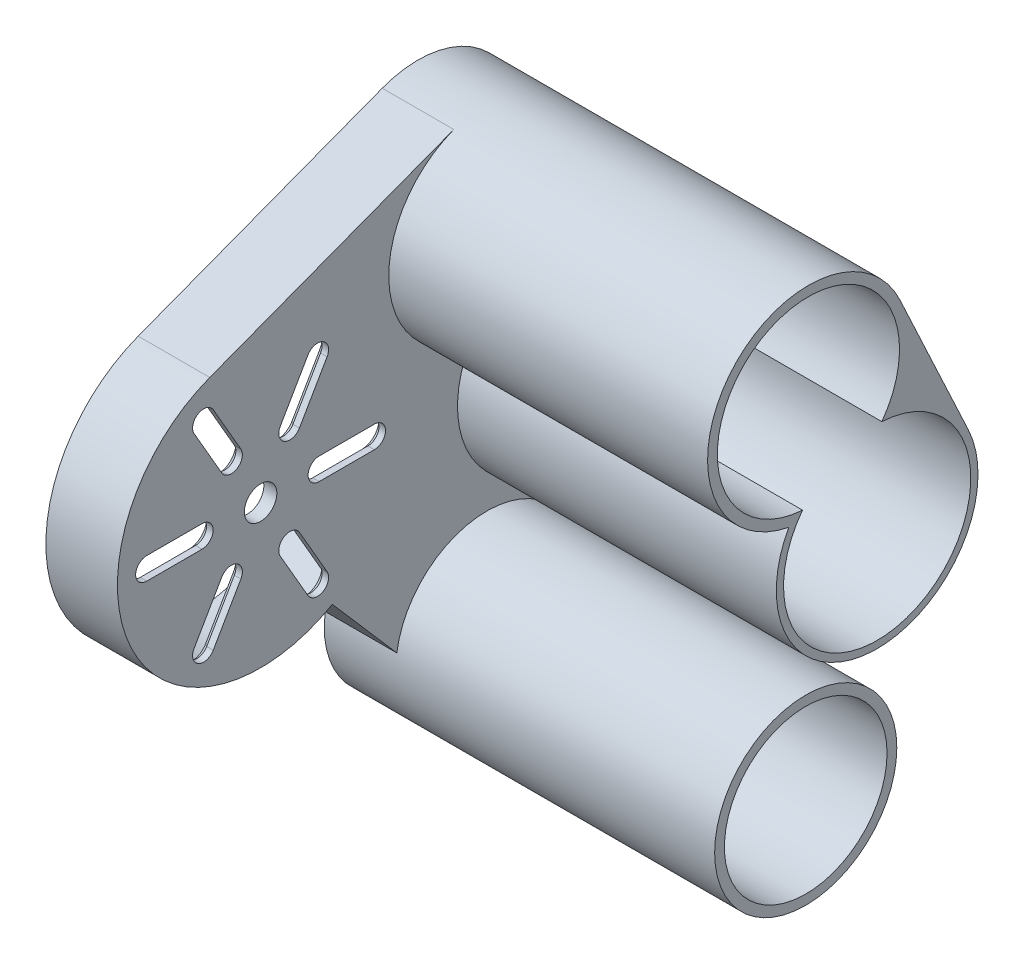
SolidWorks part; units mm, degrees
material "ABS"
ref_plane "Front Plane" through (0, 0, 0) normal (0, 0, 1) x (1, 0, 0)
ref_plane "Top Plane" through (0, 0, 0) normal (0, 1, 0) x (1, 0, 0)
ref_plane "Right Plane" through (0, 0, 0) normal (1, 0, 0) x (0, 0, -1)
sketch "Sketch1" plane through (0, 0, 0) normal (1, 0, 0) x (0, 0, -1)
  line L0 (-34.7866, 32.5023) -> (0.4149, 52.8259) construction
  line L1 (0.4149, 52.8259) -> (10.9803, 30.1682) construction
  line L2 (10.9803, 30.1682) -> (0, 0) construction
  line L3 (-34.7866, 32.5023) -> (-57.7866, 32.5023) construction
  line L4 (-43.7866, 32.5023) -> (-52.2866, 32.5023) construction
  line L5 (-43.7866, 30.8023) -> (-52.2866, 30.8023)
  line L6 (-43.7866, 34.2023) -> (-52.2866, 34.2023)
  line L9 (-23.7656, 13.4619) -> (-13.8521, 2.0298)
  line L12 (7.7696, 45.332) -> (1.428, 42.3749) construction
  line L13 (10.6233, 41.1624) -> (2.7877, 37.5086) construction
  line L14 (14.4626, 59.3765) -> (25.0281, 36.7188)
  line L15 (13.1053, -4.9244) -> (22.3217, 19.603)
  line L16 (-39.2866, 40.2965) -> (-43.5366, 47.6578) construction
  line L17 (-40.7588, 39.4465) -> (-45.0088, 46.8078)
  line L18 (-37.8144, 41.1465) -> (-42.0644, 48.5078)
  line L19 (-30.2866, 40.2965) -> (-26.0366, 47.6578) construction
  line L20 (-31.7588, 41.1465) -> (-27.5088, 48.5078)
  line L21 (-28.8144, 39.4465) -> (-24.5644, 46.8078)
  line L22 (-25.7866, 32.5023) -> (-17.2866, 32.5023) construction
  line L23 (-25.7866, 34.2023) -> (-17.2866, 34.2023)
  line L24 (-25.7866, 30.8023) -> (-17.2866, 30.8023)
  line L25 (-30.2866, 24.7081) -> (-26.0366, 17.3469) construction
  line L26 (-28.8144, 25.5581) -> (-24.5644, 18.1969)
  line L27 (-31.7588, 23.8581) -> (-27.5088, 16.4969)
  line L28 (-39.2866, 24.7081) -> (-43.5366, 17.3469) construction
  line L29 (-37.8144, 23.8581) -> (-42.0644, 16.4969)
  line L30 (-40.7588, 25.5581) -> (-45.0088, 18.1969)
  line L31 (-39.2866, 40.2965) -> (-34.7866, 32.5023) construction
  line L32 (-34.7866, 32.5023) -> (-30.2866, 40.2965) construction
  line L33 (-25.7866, 32.5023) -> (-34.7866, 32.5023) construction
  line L34 (-30.2866, 24.7081) -> (-34.7866, 32.5023) construction
  line L35 (-39.2866, 24.7081) -> (-34.7866, 32.5023) construction
  line L36 (-42.5983, 53.0687) -> (-5.0888, 67.3159)
  line L37 (0.3482, 32.9891) -> (-7.8517, 2.0832) construction
  line L38 (7.3539, -3.4512) -> (20.9383, 25.4949) construction
  line L41 (0, 0) -> (-13.8521, 2.0298) construction
  line L43 (0, 0) -> (41.0697, 0) construction
  arc A4 (-43.7866, 30.8023) -> (-43.7866, 34.2023) centre (-43.7866, 32.5023) ccw
  arc A5 (-52.2866, 34.2023) -> (-52.2866, 30.8023) centre (-52.2866, 32.5023) ccw
  circle A6 centre (-34.7866, 32.5023) radius 2.5
  circle A7 centre (0, 0) radius 2.5
  arc A8 (-13.8521, 2.0298) -> (13.1053, -4.9244) centre (0, 0) ccw
  circle A9 centre (-34.7866, 32.5023) radius 22 construction
  circle A11 centre (10.9803, 30.1682) radius 2.5
  circle A12 centre (-34.7866, 32.5023) radius 23 construction
  circle A14 centre (0.4149, 52.8259) radius 2.5
  circle A15 centre (0.4149, 52.8259) radius 15.5 construction
  circle A16 centre (0.4149, 52.8259) radius 10.5 construction
  circle A17 centre (10.9803, 30.1682) radius 11 construction
  circle A18 centre (10.9803, 30.1682) radius 15.5 construction
  arc A19 (-40.7588, 39.4465) -> (-37.8144, 41.1465) centre (-39.2866, 40.2965) ccw
  arc A20 (-42.0644, 48.5078) -> (-45.0088, 46.8078) centre (-43.5366, 47.6578) ccw
  arc A21 (-31.7588, 41.1465) -> (-28.8144, 39.4465) centre (-30.2866, 40.2965) ccw
  arc A22 (-24.5644, 46.8078) -> (-27.5088, 48.5078) centre (-26.0366, 47.6578) ccw
  arc A23 (-25.7866, 34.2023) -> (-25.7866, 30.8023) centre (-25.7866, 32.5023) ccw
  arc A24 (-17.2866, 30.8023) -> (-17.2866, 34.2023) centre (-17.2866, 32.5023) ccw
  arc A25 (-28.8144, 25.5581) -> (-31.7588, 23.8581) centre (-30.2866, 24.7081) ccw
  arc A26 (-27.5088, 16.4969) -> (-24.5644, 18.1969) centre (-26.0366, 17.3469) ccw
  arc A27 (-37.8144, 23.8581) -> (-40.7588, 25.5581) centre (-39.2866, 24.7081) ccw
  arc A28 (-45.0088, 18.1969) -> (-42.0644, 16.4969) centre (-43.5366, 17.3469) ccw
  circle A29 centre (0, 0) radius 8.1234 construction
  arc A30 (-5.0888, 67.3159) -> (14.4626, 59.3765) centre (0.4149, 52.8259) cw
  circle A31 centre (0, 0) radius 14 construction
  arc A32 (25.0281, 36.7188) -> (22.3217, 19.603) centre (10.9803, 30.1682) cw
  circle A33 centre (-34.7866, 32.5023) radius 9 construction
  circle A34 centre (-34.7866, 32.5023) radius 17.5 construction
  arc A35 (-42.5983, 53.0687) -> (-23.7656, 13.4619) centre (-34.7866, 32.5023) ccw
  point P12 (-48.0366, 32.5023)
  point P44 (-41.4116, 43.9771)
  point P51 (-28.1616, 43.9771)
  point P58 (-21.5366, 32.5023)
  point P65 (-28.1616, 21.0275)
  point P72 (-41.4116, 21.0275)
  dimension "D2" = 5
  dimension "D3" = 5
  dimension "D4" = 32.1043
  dimension "D5" = 25
  dimension "D7" = 44
  dimension "D9" = 21
  dimension "D11" = 31
  dimension "D12" = 16.2468
  dimension "D16" = 70
  dimension "D17" = 18
  dimension "D8" = 31
  dimension "D10" = 22
  dimension "D13" = 28
  dimension "D14" = 35
  dimension "D20" = 46
  dimension "D6" = 135
  dimension "D15" = 85
  dimension "D19" = 3.4
  dimension "D18" = 6
extrude "Boss-Extrude1" add sketch "Sketch1" along normal blind 50 and the other way blind 10
sketch "Sketch2" plane through (-10, 0, 0) normal (-1, 0, 0) x (0, 0, 1)
  line L0 (38.6871, 54.5543) -> (38.1899, 53.2456) construction
  line L1 (42.5983, 53.0687) -> (5.0888, 67.3159) construction
  line L2 (-13.1053, -4.9244) -> (-22.3217, 19.603) construction
  line L3 (27.472, 13.2447) -> (10.0077, 19.8781)
  line L4 (10.0077, 19.8781) -> (12.4846, 1.7013)
  line L6 (42.1012, 51.76) -> (4.5917, 66.0071)
  line L11 (-11.7948, -4.432) -> (-21.4204, 21.1844)
  line L12 (-23.5382, 35.8254) -> (-13.2706, 58.6173)
  arc A0 (27.472, 13.2447) -> (42.1012, 51.76) centre (34.7866, 32.5023) ccw
  arc A2 (-11.7948, -4.432) -> (12.4846, 1.7013) centre (0, 0) ccw
  arc A3 (-21.4204, 21.1844) -> (-23.5382, 35.8254) centre (-10.9803, 30.1682) cw
  arc A4 (-13.2706, 58.6173) -> (4.5917, 66.0071) centre (-0.4149, 52.8259) cw
  dimension "D1" = 1.4
  dimension "D2" = 1.4
extrude "Cut-Extrude1" cut sketch "Sketch2" against normal blind 9
sketch "Sketch3" plane through (50, 0, 0) normal (1, 0, 0) x (0, 0, -1)
  line L1 (-42.5983, 53.0687) -> (-5.0888, 67.3159) construction
  line L2 (22.3217, 19.603) -> (13.1053, -4.9244)
  line L3 (-5.0888, 67.3159) -> (-55.4269, 48.1961)
  line L4 (-55.4269, 48.1961) -> (-58.2869, 17.3245)
  line L5 (-58.2869, 17.3245) -> (-13.8521, 2.0298)
  line L6 (14.4626, 59.3765) -> (25.0281, 36.7188)
  arc A0 (-2.6089, 37.6237) -> (-5.0888, 67.3159) centre (0.4149, 52.8259) cw
  circle A1 centre (0.4149, 52.8259) radius 15.5 construction
  arc A2 (-2.6089, 37.6237) -> (22.3217, 19.603) centre (10.9803, 30.1682) ccw
  circle A3 centre (10.9803, 30.1682) radius 15.5 construction
  arc A4 (13.1053, -4.9244) -> (-13.8521, 2.0298) centre (0, 0) ccw
  circle A6 centre (0.4149, 52.8259) radius 14
  circle A7 centre (10.9803, 30.1682) radius 14.3914
  circle A8 centre (0, 0) radius 12.5
  arc A9 (14.4626, 59.3765) -> (14.004, 45.3704) centre (0.4149, 52.8259) cw
  arc A10 (25.0281, 36.7188) -> (14.004, 45.3704) centre (10.9803, 30.1682) ccw
  arc A11 (-42.5983, 53.0687) -> (-23.7656, 13.4619) centre (-34.7866, 32.5023) ccw construction
extrude "Cut-Extrude2" cut sketch "Sketch3" against normal blind 49
chamfer "Chamfer1" distance 1 angle 45 24 edges at (-1, 21.8775, 26.6894) (-1, 26.1803, 31.1366) (-1, 15.8746, 25.1866) (-1, 20.1775, 29.6338) (-1, 20.1775, 39.9394) (-1, 26.1803, 38.4366) (-1, 15.8746, 44.3866) (-1, 21.8775, 42.8838) (-1, 30.8023, 48.0366) (-1, 32.5023, 42.0866) (-1, 32.5023, 53.9866) (-1, 34.2023, 48.0366) (-1, 43.1271, 42.8838) (-1, 38.8243, 38.4366) (-1, 49.13, 44.3866) (-1, 44.8271, 39.9394) (-1, 49.13, 25.1866) (-1, 44.8271, 29.6338) (-1, 38.8243, 31.1366) (-1, 43.1271, 26.6894) (-1, 32.5023, 27.4866) (-1, 30.8023, 21.5366) (-1, 32.5023, 15.5866) (-1, 34.2023, 21.5366)
chamfer "Chamfer3" distance 0.25 angle 45 10 edges at (-1, 65.8549, -5.8051) (-1, 47.2213, -18.4044) (-1, 28.1964, -24.6117) (-1, 8.3762, -16.6076) (-1, -12.2163, 3.086) (-1, 10.7897, 11.2461) (-1, 16.5614, 18.7398) (-1, 25.1877, 54.0442) (-1, 58.8835, 23.3465) (-5.5, 19.8781, 10.0077)
